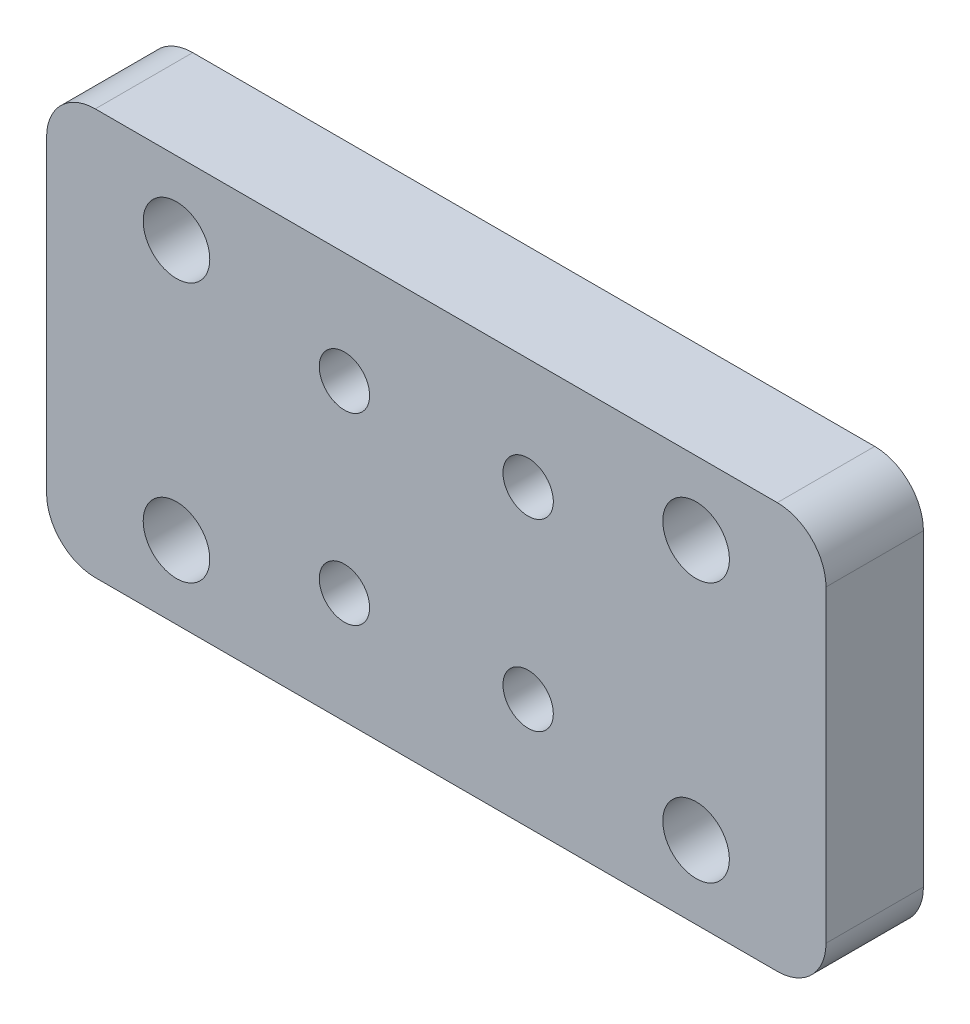
SolidWorks part; units mm, degrees
material "ABS"
ref_plane "Front Plane" through (0, 0, 0) normal (0, 0, 1) x (1, 0, 0)
ref_plane "Top Plane" through (0, 0, 0) normal (0, 1, 0) x (1, 0, 0)
ref_plane "Right Plane" through (0, 0, 0) normal (1, 0, 0) x (0, 0, -1)
sketch "Sketch1" plane through (0, 0, 0) normal (0, 0, 1) x (1, 0, 0)
  line L2 (-26.3664, -1.9656) -> (21.6336, -1.9656) construction
  line L3 (-2.3664, 10.5344) -> (-2.3664, -14.4656) construction
  line L5 (13.6336, -9.9656) -> (-18.3664, -9.9656) construction
  line L6 (13.6336, 6.0344) -> (-18.3664, 6.0344) construction
  line L7 (5.6336, -9.9656) -> (-10.3664, -9.9656) construction
  line L8 (5.6336, -9.9656) -> (5.6336, 6.0344) construction
  line L9 (5.6336, 6.0344) -> (-10.3664, 6.0344) construction
  line L10 (-10.3664, -9.9656) -> (-10.3664, 6.0344) construction
  line L11 (5.6336, -9.9656) -> (-10.3664, 6.0344) construction
  line L12 (5.6336, 6.0344) -> (-10.3664, -9.9656) construction
  line L13 (21.6336, -14.4656) -> (-26.3664, -14.4656)
  line L14 (21.6336, -14.4656) -> (21.6336, 10.5344)
  line L15 (21.6336, 10.5344) -> (-26.3664, 10.5344)
  line L16 (-26.3664, -14.4656) -> (-26.3664, 10.5344)
  circle A8 centre (-2.3664, -1.9656) radius 8 construction
  circle A10 centre (-8.0233, 3.6912) radius 1.55
  circle A13 centre (-8.0233, -7.6225) radius 1.55
  circle A14 centre (3.2904, -7.6225) radius 1.55
  circle A15 centre (3.2904, 3.6912) radius 1.55
  circle A16 centre (-18.3664, 6.0344) radius 2.05
  circle A17 centre (13.6336, 6.0344) radius 2.05
  circle A18 centre (13.6336, -9.9656) radius 2.05
  circle A19 centre (-18.3664, -9.9656) radius 2.05
  point P0 (-8.0233, 3.6912)
  point P1 (3.2904, -7.6225)
  point P3 (3.2904, 3.6912)
  point P4 (-8.0233, -7.6225)
  point P9 (-2.3664, -1.9656)
  point P18 (-2.3664, -1.9656)
  point P31 (-2.3664, -9.9656)
  point P32 (-2.3664, -9.9656)
  point P35 (-2.3664, 6.0344)
  point P39 (0, 0)
  dimension "D3" = 3.1
  dimension "D4" = 4.1
  dimension "D5" = 32
  dimension "D10" = 25
  dimension "D2" = 16
  dimension "D8" = 16
  dimension "D9" = 16
  dimension "D11" = 48
extrude "Boss-Extrude1" add sketch "Sketch1" along normal blind 6
fillet "Fillet1" radius 3 1 edges at (21.6336, -14.4656, 3)
fillet "Fillet2" radius 3 1 edges at (-26.3664, -14.4656, 3)
fillet "Fillet3" radius 3 1 edges at (21.6336, 10.5344, 3)
fillet "Fillet4" radius 3 1 edges at (-26.3664, 10.5344, 3)
